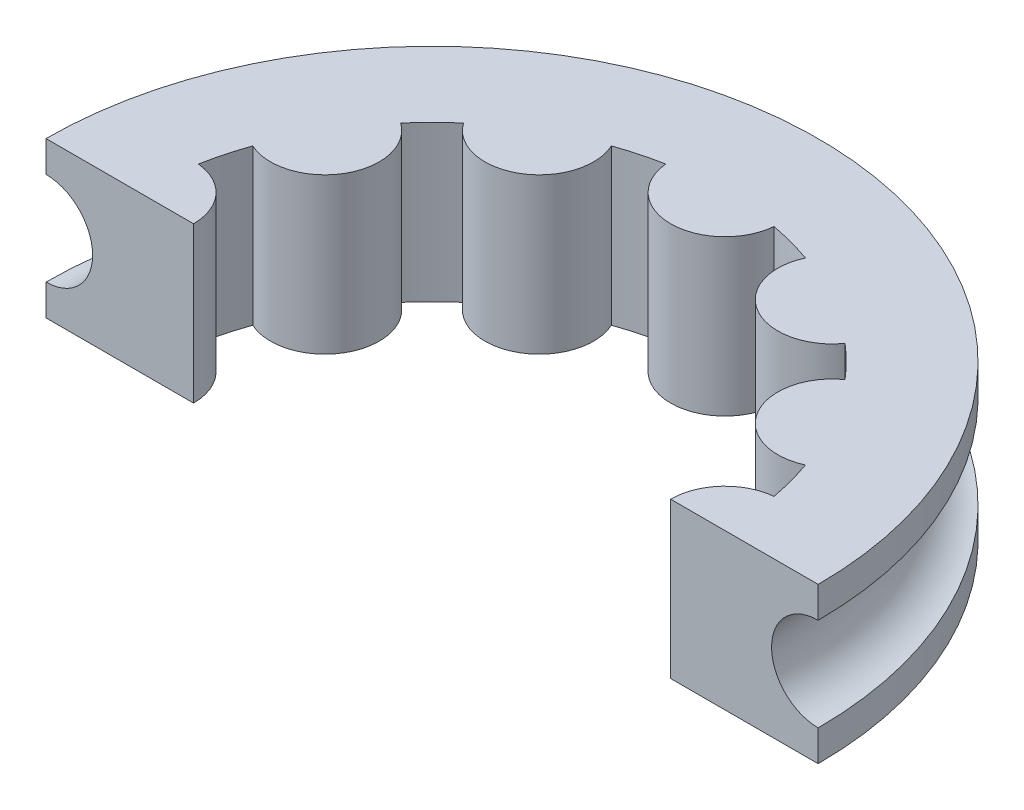
SolidWorks part; units mm, degrees
ref_plane "Front Plane" through (0, 0, 0) normal (0, 0, 1) x (1, 0, 0)
ref_plane "Top Plane" through (0, 0, 0) normal (0, 1, 0) x (1, 0, 0)
ref_plane "Right Plane" through (0, 0, 0) normal (1, 0, 0) x (0, 0, -1)
sketch "Sketch1" plane through (0, 0, 0) normal (0, 1, 0) x (1, 0, 0)
  circle A1 centre (-10, 0) radius 1.75
  circle A2 centre (-8.737, 4.7137) radius 1.75
  circle A3 centre (-5.2863, 8.1644) radius 1.75
  circle A4 centre (-0.5726, 9.4274) radius 1.75
  circle A5 centre (4.1412, 8.1644) radius 1.75
  circle A6 centre (7.5918, 4.7137) radius 1.75
  circle A7 centre (8.8549, 0) radius 1.75
  circle A8 centre (7.5918, -4.7137) radius 1.75
  circle A9 centre (4.1412, -8.1644) radius 1.75
  circle A10 centre (-0.5726, -9.4274) radius 1.75
  circle A11 centre (-5.2863, -8.1644) radius 1.75
  circle A12 centre (-8.737, -4.7137) radius 1.75
  circle A13 centre (-0.5726, 0) radius 9.4274
  circle A14 centre (-0.5726, 0) radius 12.4274
  dimension "D1" = 3
  dimension "D2" = 3.5
  dimension "D4" = 4.88
  dimension "D3" = 12
extrude "Boss-Extrude1" add sketch "Sketch1" along normal blind 5 contours A14 A13 A10 A11 A12 A1 A2 A3 A4 A5 A6 A7 A8 A9 | A13 A12 | A12 A13 | A1 A13 | A13 A1 | A2 A13 | A13 A2 | A3 A13 | A13 A3 | A4 A13 | A13 A4 | A5 A13 | A13 A5 | A6 A13 | A13 A6 | A7 A13 | A13 A7 | A8 A13 | A13 A8 | A9 A13 | A13 A9 | A10 A13 | A13 A10 | A11 A13 | A13 A11
sketch "Sketch7" plane through (0, 5, 0) normal (0, 1, 0) x (1, 0, 0)
  line L0 (13.3005, 0) -> (-14.2053, 0)
  line L1 (-2.75, 0) -> (2.75, 0) construction
  line L2 (-14.2053, 0) -> (-13.3923, -15.4494)
  line L3 (-13.3923, -15.4494) -> (9.4389, -14.772)
  line L4 (9.4389, -14.772) -> (13.3005, 0)
extrude "Cut-Extrude1" cut sketch "Sketch7" against normal through all
sketch "Sketch8" plane through (0, 0, 0) normal (0, 0, 1) x (1, 0, 0)
  line L0 (7.1049, 4) -> (11.8549, 4)
  line L1 (7.1049, 0) -> (7.1049, 5) construction
  line L2 (11.8549, 5) -> (11.8549, 0) construction
  line L3 (7.1049, 2.5) -> (11.8549, 2.5) construction
  line L4 (11.8549, 5) -> (7.1049, 5) construction
  line L5 (7.1049, 1) -> (11.8549, 1)
  circle A0 centre (11.8549, 2.5) radius 1.5
  dimension "D1" = 1
sketch "Sketch9" plane through (0, 5, 0) normal (0, 1, 0) x (1, 0, 0)
  line L0 (-0.5726, 12.4274) -> (-0.5726, 0) construction
  line L1 (-2.75, 0) -> (2.75, 0) construction
sketch "Sketch10" plane through (0, 0, 0) normal (0, 0, 1) x (1, 0, 0)
  line L0 (-0.5726, 5) -> (-0.5726, 0.8777) construction
  point P2 (0, 0)
revolve "Cut-Revolve2" cut sketch "Sketch8" angle 360 about L0
equation "\"HOLE_SIZE\"= 3.5mm"
equation "\"DIST\"= 4.88mm"
